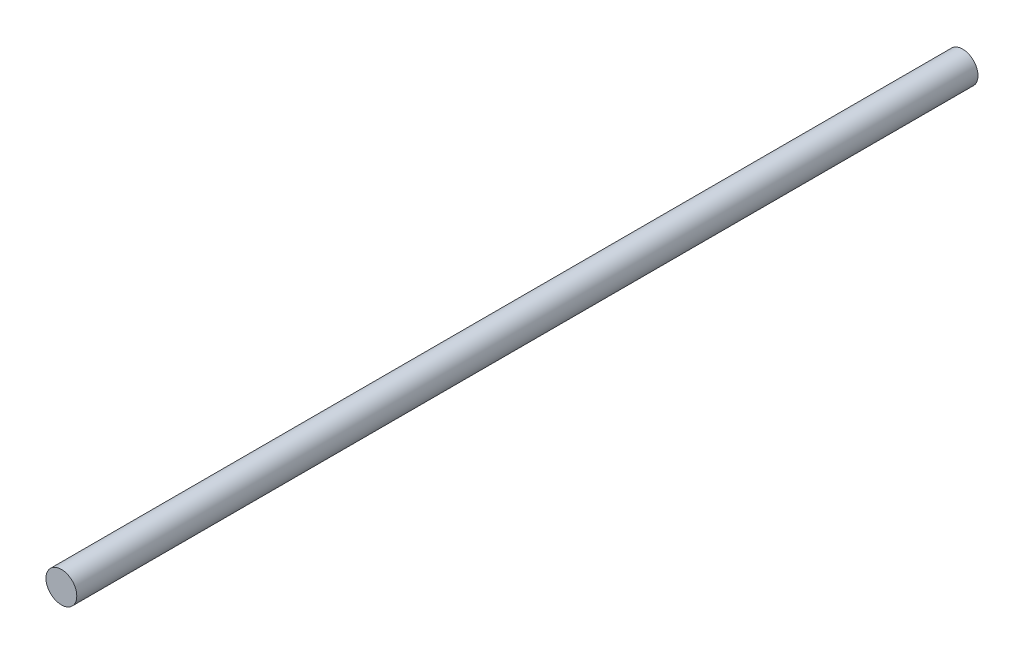
SolidWorks part; units mm, degrees
ref_plane "Front Plane" through (0, 0, 0) normal (0, 0, 1) x (1, 0, 0)
ref_plane "Top Plane" through (0, 0, 0) normal (0, 1, 0) x (1, 0, 0)
ref_plane "Right Plane" through (0, 0, 0) normal (1, 0, 0) x (0, 0, -1)
sketch "Sketch1" plane through (0, 0, 0) normal (0, 0, 1) x (1, 0, 0)
  circle A0 centre (0, 0) radius 5.08
extrude "Boss-Extrude1" add sketch "Sketch1" along normal blind 297.18
